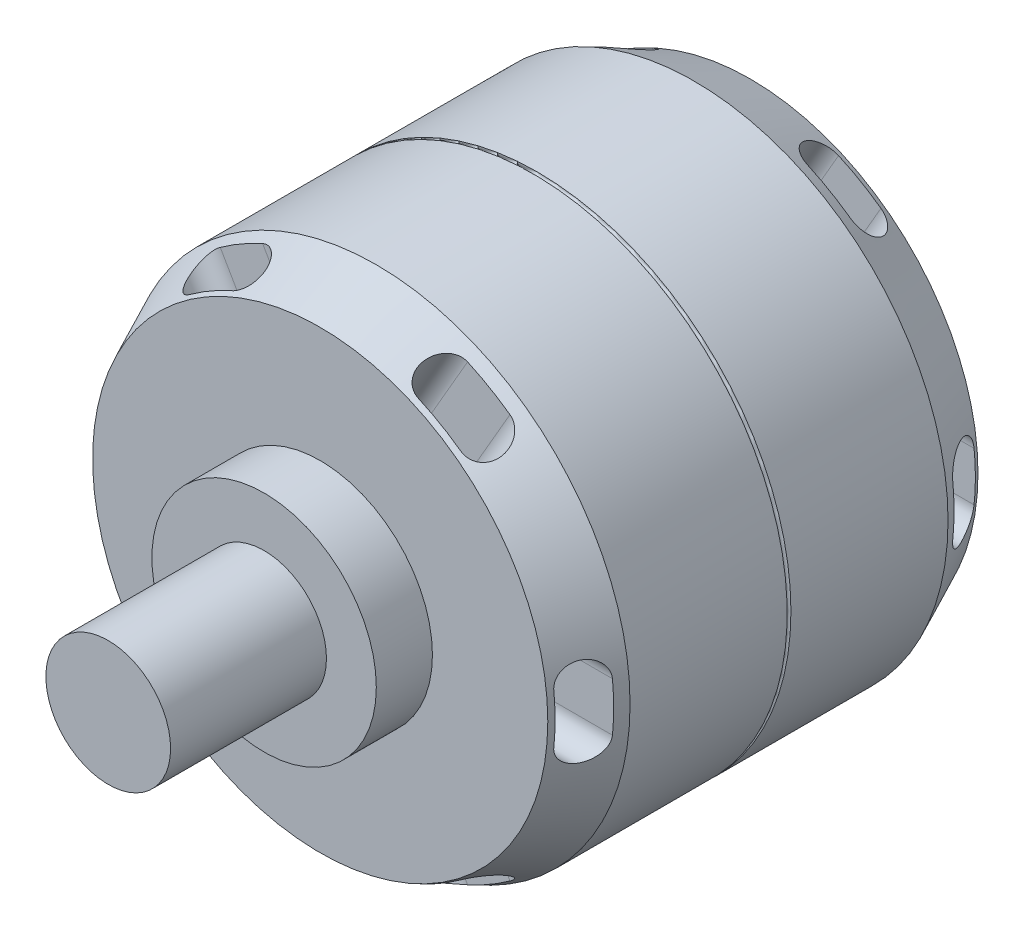
SolidWorks part; units mm, degrees
material "Custom Plastic"
ref_plane "Front Plane" through (0, 0, 0) normal (0, 0, 1) x (1, 0, 0)
ref_plane "Top Plane" through (0, 0, 0) normal (0, 1, 0) x (1, 0, 0)
ref_plane "Right Plane" through (0, 0, 0) normal (1, 0, 0) x (0, 0, -1)
sketch "Sketch1" plane through (0, 0, 0) normal (0, 0, 1) x (1, 0, 0)
  circle A0 centre (0, 0) radius 40.7
  dimension "D1" = 81.4
extrude "Boss-Extrude1" add sketch "Sketch1" along normal blind 51
sketch "Sketch3" plane through (0, 0, 51) normal (0, 0, 1) x (1, 0, 0)
  circle A1 centre (0, 0) radius 40.7
  circle A2 centre (0, 0) radius 40.7
  dimension "D1" = 0
extrude "Boss-Extrude2" add sketch "Sketch3" along normal blind 9 draft 25
sketch "Sketch4" plane through (0, 0, 0) normal (1, 0, 0) x (0, 0, -1)
  line L0 (0, 0) -> (-56, 0) construction
  line L1 (-56, 3.9242) -> (-56, -3.9242) construction
  line L2 (-52.7976, 3.9242) -> (-52.7976, -3.9242)
  line L3 (-59.2024, 3.9242) -> (-59.2024, -3.9242)
  arc A0 (-52.7976, 3.9242) -> (-59.2024, 3.9242) centre (-56, 3.9242) ccw
  arc A1 (-59.2024, -3.9242) -> (-52.7976, -3.9242) centre (-56, -3.9242) ccw
  point P5 (-56, 0)
  dimension "D1" = 56
extrude "Cut-Extrude1" cut sketch "Sketch4" against normal through all both and the other way through all
pattern_circular "CirPattern1" count 6 over 360 about axis through (0, 0, 52.7976) along (0, 0, -1) of "Cut-Extrude1", "Boss-Extrude2"
ref_plane "Plane1" through (0, 0, 25.5) normal (0, 0, 1) x (1, 0, 0)
mirror "Mirror1" about plane through (0, 0, 25.5) normal (0, 0, 1) of "CirPattern1", "Cut-Extrude1", "Boss-Extrude2"
sketch "Sketch5" plane through (0, 0, 60) normal (0, 0, 1) x (1, 0, 0)
  circle A0 centre (0, 0) radius 18
  dimension "D1" = 36
sketch "Sketch6" plane through (0, 0, 0) normal (1, 0, 0) x (0, 0, -1)
  line L0 (-51, -40.7) -> (0, -40.7) construction
  line L1 (0, 0) -> (-60, 0) construction
  circle A0 centre (-25.5, -40.7) radius 0.3
  dimension "D1" = 0.6
revolve "Cut-Revolve1" cut sketch "Sketch6" angle 360 about L1
extrude "Boss-Extrude3" add sketch "Sketch5" along normal blind 9
sketch "Sketch7" plane through (0, 0, 69) normal (0, 0, 1) x (1, 0, 0)
  circle A0 centre (0, 0) radius 10
  dimension "D1" = 20
extrude "Boss-Extrude4" add sketch "Sketch7" along normal blind 25
sketch "Sketch8" plane through (0, 0, -9) normal (0, 0, -1) x (-1, 0, 0)
  point P0 (0, 0)
